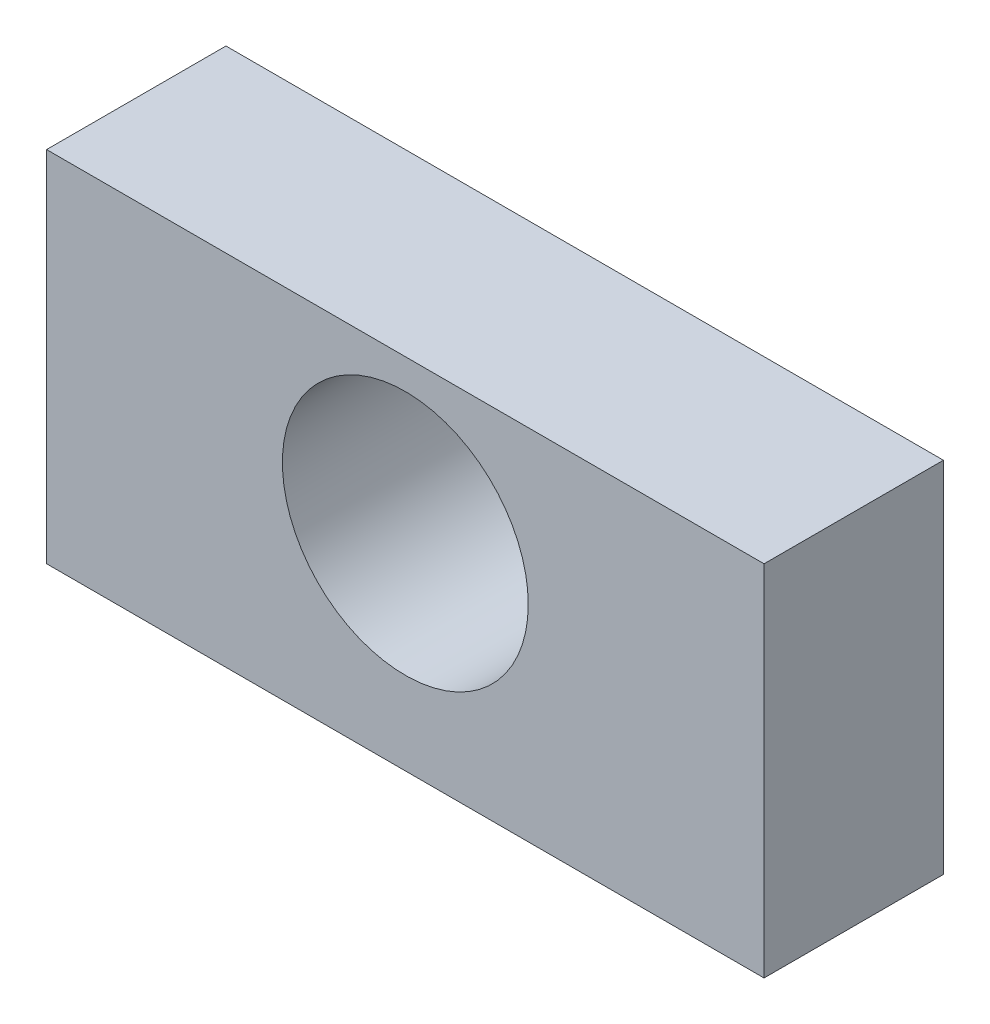
SolidWorks part; units mm, degrees
ref_plane "Front Plane" through (0, 0, 0) normal (0, 0, 1) x (1, 0, 0)
ref_plane "Top Plane" through (0, 0, 0) normal (0, 1, 0) x (1, 0, 0)
ref_plane "Right Plane" through (0, 0, 0) normal (1, 0, 0) x (0, 0, -1)
sketch "Sketch1" plane through (0, 0, 0) normal (0, 0, 1) x (1, 0, 0)
  line L1 (-9.525, -4.7625) -> (9.525, -4.7625)
  line L2 (-9.525, -4.7625) -> (-9.525, 4.7625)
  line L3 (-9.525, 4.7625) -> (9.525, 4.7625)
  line L4 (9.525, -4.7625) -> (9.525, 4.7625)
  line L5 (-9.525, -4.7625) -> (9.525, 4.7625) construction
  line L6 (-9.525, 4.7625) -> (9.525, -4.7625) construction
  point P0 (0, 0)
  dimension "D1" = 19.05
  dimension "D2" = 9.525
extrude "Extrude1" add sketch "Sketch1" along normal blind 4.7625
sketch "Sketch2" plane through (0, 0, 4.7625) normal (0, 0, 1) x (1, 0, 0)
  line L0 (0, 4.7625) -> (0, 0.6985) construction
  line L1 (9.525, 4.7625) -> (-9.525, 4.7625) construction
  dimension "D1" = 4.064
hole_wizard "1/4 Clearance Hole1" positions "3DSketch2" profile "Sketch4" hole size "1/4" standard "Ansi Inch"
sketch3d "3DSketch2"
  point P2 (0, 0.6985, 4.7625)
sketch "Sketch4" plane through (0, 0.6985, 4.7625) normal (1, 0, 0) x (0, -1, 0)
  line L0 (0, 0) -> (0, 17.2011)
  line L1 (0, 17.2011) -> (3.2639, 15.24)
  line L2 (3.2639, 15.24) -> (3.2639, 0)
  line L5 (3.2639, 0) -> (0, 0)
  line L10 (0, 17.2011) -> (-3.2639, 15.24) construction
  line L11 (0, -6.35) -> (0, 107.95) construction
  dimension "Hole Dia." = 6.5278
  dimension "Hole Depth" = 15.24
  dimension "Drill Angle" = 118
